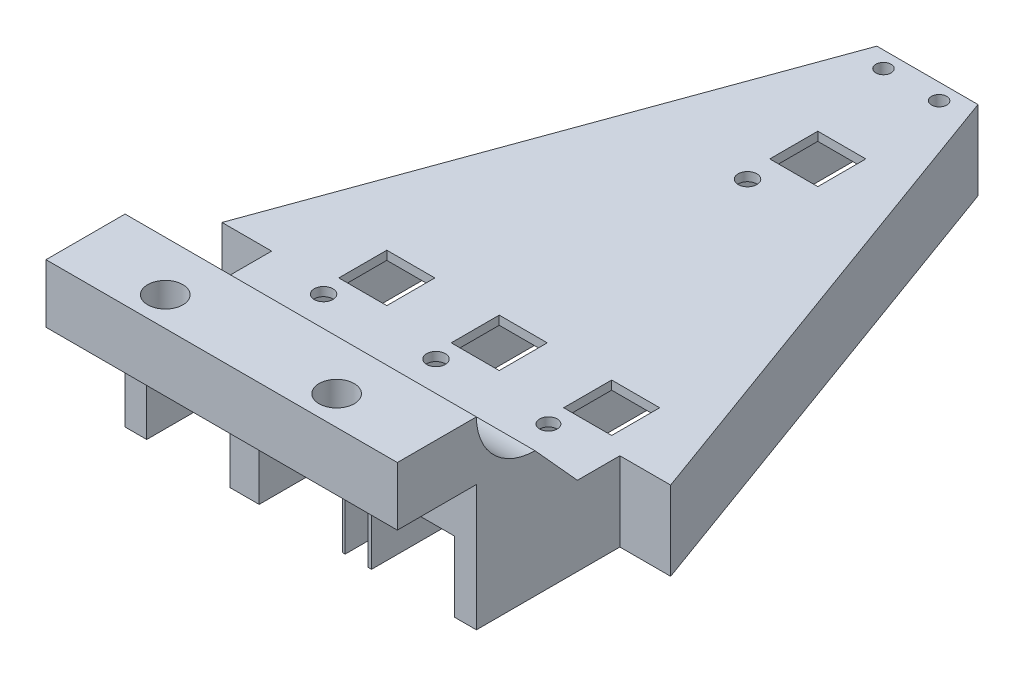
SolidWorks part; units mm, degrees
ref_plane "Front Plane" through (0, 0, 0) normal (0, 0, 1) x (1, 0, 0)
ref_plane "Top Plane" through (0, 0, 0) normal (0, 1, 0) x (1, 0, 0)
ref_plane "Right Plane" through (0, 0, 0) normal (1, 0, 0) x (0, 0, -1)
sketch "Sketch2" plane through (0, 0, 0) normal (0, 1, 0) x (1, 0, 0)
  line L1 (-15.37, -5) -> (44.63, -5)
  line L2 (-15.37, -5) -> (-15.37, 8.5)
  line L3 (-15.37, 8.5) -> (44.63, 8.5)
  line L4 (44.63, -5) -> (44.63, 8.5)
  circle A0 centre (0, 0) radius 1.75
  circle A1 centre (29.264, 0) radius 1.75
  point P12 (14.63, -5)
  dimension "D2" = 3.5
  dimension "D1" = 29.264
  dimension "D3" = 5
  dimension "D4" = 14.63
  dimension "D5" = 60
  dimension "D6" = 8.5
extrude "Boss-Extrude1" add sketch "Sketch2" along normal blind 10
sketch "Sketch4" plane through (0, 0, 0) normal (0, 1, 0) x (1, 0, 0)
  line L0 (-15.37, 8.5) -> (-15.37, 33.5337)
  line L1 (-15.37, 33.5337) -> (-23.8471, 33.5337)
  line L2 (-23.8471, 33.5337) -> (5.995, 115.5242)
  line L3 (53.3011, 33.0007) -> (23.265, 115.5242)
  line L4 (53.3011, 33.0007) -> (44.63, 33.0007)
  line L5 (44.63, 33.0007) -> (44.63, 8.5)
  line L6 (-15.37, -5) -> (44.63, -5) construction
  line L7 (7.53, 56.7) -> (21.73, 56.7)
  line L8 (7.53, 56.7) -> (7.53, 24.5)
  line L9 (7.53, 24.5) -> (21.73, 24.5)
  line L10 (21.73, 56.7) -> (21.73, 24.5)
  line L11 (26.73, 56.7) -> (40.93, 56.7)
  line L12 (26.73, 56.7) -> (26.73, 24.5)
  line L13 (26.73, 24.5) -> (40.93, 24.5)
  line L14 (40.93, 56.7) -> (40.93, 24.5)
  line L15 (-11.67, 56.7) -> (2.53, 56.7)
  line L16 (-11.67, 56.7) -> (-11.67, 24.5)
  line L17 (-11.67, 24.5) -> (2.53, 24.5)
  line L18 (2.53, 56.7) -> (2.53, 24.5)
  line L19 (7.53, 109.9) -> (21.73, 109.9)
  line L20 (7.53, 109.9) -> (7.53, 77.7)
  line L21 (7.53, 77.7) -> (21.73, 77.7)
  line L22 (21.73, 109.9) -> (21.73, 77.7)
  line L23 (23.265, 115.5242) -> (5.995, 115.5242)
  line L24 (44.63, 8.5) -> (-15.37, 8.5) construction
  line L25 (9.88, 112.7697) -> (19.38, 112.7697) construction
  circle A0 centre (9.88, 112.7697) radius 1.3
  circle A1 centre (19.38, 112.7697) radius 1.3
  point P23 (14.63, -5)
  point P24 (14.63, 56.7)
  point P29 (14.63, 109.9)
  point P30 (14.63, 77.7)
  point P31 (14.63, 115.5242)
  point P39 (14.63, 112.7697)
  dimension "D9" = 2.6
  dimension "D10" = 2.6
  dimension "D1" = 32.2
  dimension "D2" = 14.2
  dimension "D3" = 5
  dimension "D4" = 5
  dimension "D5" = 16
  dimension "D6" = 21
  dimension "D7" = 70
  dimension "D8" = 70
  dimension "D11" = 9.5
  dimension "D12" = 14.2
  dimension "D13" = 32.2
sketch "Sketch5" plane through (0, 0, 0) normal (0, 1, 0) x (1, 0, 0)
  line L0 (-15.37, 8.5) -> (-15.37, 33.5337) construction
  line L1 (-15.37, 33.5337) -> (-23.8471, 33.5337) construction
  line L2 (53.3011, 33.0007) -> (44.63, 33.0007) construction
  line L3 (44.63, 33.0007) -> (44.63, 8.5) construction
  line L4 (53.3011, 33.0007) -> (23.265, 115.5242) construction
  line L5 (23.265, 115.5242) -> (5.995, 115.5242) construction
  line L6 (-23.8471, 33.5337) -> (5.995, 115.5242) construction
  line L7 (-15.37, 8.5) -> (-15.37, 33.5337)
  line L8 (-15.37, 33.5337) -> (-23.8471, 33.5337)
  line L9 (53.3011, 33.0007) -> (44.63, 33.0007)
  line L10 (44.63, 33.0007) -> (44.63, 8.5)
  line L11 (53.3011, 33.0007) -> (23.265, 115.5242)
  line L12 (23.265, 115.5242) -> (5.995, 115.5242)
  line L13 (-23.8471, 33.5337) -> (5.995, 115.5242)
  line L14 (44.63, 8.5) -> (-15.37, 8.5) construction
  line L15 (44.63, 8.5) -> (-15.37, 8.5)
extrude "Boss-Extrude2" add sketch "Sketch5" against normal blind 21.5 separate body
sketch "Sketch8" plane through (-15.37, 0, 0) normal (-1, 0, 0) x (0, 0, 1)
  line L1 (-33.0007, 0) -> (-8.5, 0) construction
  line L2 (-8.5, 10) -> (-8.5, 0) construction
  line L3 (-18.5, 0) -> (-8.5, 0)
  line L4 (-8.5, 10) -> (-8.5, 0)
  arc A0 (-18.5, 0) -> (-8.5, 10) centre (-18.5, 10) ccw
extrude "Boss-Extrude3" add sketch "Sketch8" against normal up to surface (60 mm away) up to face at (44.63, 5, -1.75)
sketch "Sketch10" plane through (0, 0, 0) normal (0, 1, 0) x (1, 0, 0)
  line L0 (9.88, 112.7697) -> (19.38, 112.7697) construction
  line L1 (9.88, 112.7697) -> (19.38, 112.7697)
  circle A0 centre (19.38, 112.7697) radius 1.3 construction
  circle A1 centre (9.88, 112.7697) radius 1.3 construction
  circle A2 centre (19.38, 112.7697) radius 1.3
  circle A3 centre (9.88, 112.7697) radius 1.3
extrude "Cut-Extrude1" cut sketch "Sketch10" against normal through all
sketch "Sketch12" plane through (0, -21.5, 0) normal (0, -1, 0) x (1, 0, 0)
  line L0 (21.73, -109.9) -> (21.73, -77.7) construction
  line L1 (7.53, -109.9) -> (21.73, -109.9) construction
  line L2 (7.53, -77.7) -> (21.73, -77.7) construction
  line L3 (7.53, -109.9) -> (7.53, -77.7) construction
  line L4 (-11.67, -24.5) -> (2.53, -24.5) construction
  line L5 (-11.67, -56.7) -> (-11.67, -24.5) construction
  line L6 (-11.67, -56.7) -> (2.53, -56.7) construction
  line L7 (2.53, -56.7) -> (2.53, -24.5) construction
  line L8 (7.53, -56.7) -> (21.73, -56.7) construction
  line L9 (7.53, -56.7) -> (7.53, -24.5) construction
  line L10 (7.53, -24.5) -> (21.73, -24.5) construction
  line L11 (21.73, -56.7) -> (21.73, -24.5) construction
  line L12 (26.73, -24.5) -> (40.93, -24.5) construction
  line L13 (26.73, -56.7) -> (26.73, -24.5) construction
  line L14 (26.73, -56.7) -> (40.93, -56.7) construction
  line L15 (40.93, -56.7) -> (40.93, -24.5) construction
  line L16 (21.73, -109.9) -> (21.73, -77.7)
  line L17 (7.53, -109.9) -> (21.73, -109.9)
  line L18 (7.53, -77.7) -> (21.73, -77.7)
  line L19 (7.53, -109.9) -> (7.53, -77.7)
  line L20 (-11.67, -24.5) -> (2.53, -24.5)
  line L21 (-11.67, -56.7) -> (-11.67, -24.5)
  line L22 (-11.67, -56.7) -> (2.53, -56.7)
  line L23 (2.53, -56.7) -> (2.53, -24.5)
  line L24 (7.53, -56.7) -> (21.73, -56.7)
  line L25 (7.53, -56.7) -> (7.53, -24.5)
  line L26 (7.53, -24.5) -> (21.73, -24.5)
  line L27 (21.73, -56.7) -> (21.73, -24.5)
  line L28 (26.73, -24.5) -> (40.93, -24.5)
  line L29 (26.73, -56.7) -> (26.73, -24.5)
  line L30 (26.73, -56.7) -> (40.93, -56.7)
  line L31 (40.93, -56.7) -> (40.93, -24.5)
extrude "Cut-Extrude2" cut sketch "Sketch12" against normal blind 12
sketch "Sketch13" plane through (0, -21.5, 0) normal (0, -1, 0) x (1, 0, 0)
  line L0 (7.53, -109.9) -> (7.53, -77.7) construction
  line L1 (21.73, -77.7) -> (7.53, -77.7)
  line L2 (21.73, -77.7) -> (21.73, -61.7)
  line L4 (7.53, -77.7) -> (7.53, -61.7)
  line L5 (-15.37, -8.5) -> (44.63, -8.5) construction
  line L6 (26.73, -24.5) -> (40.93, -24.5)
  line L7 (26.73, -24.5) -> (26.73, -8.5)
  line L9 (40.93, -24.5) -> (40.93, -8.5)
  line L10 (40.93, -56.7) -> (40.93, -24.5) construction
  line L15 (7.53, -24.5) -> (21.73, -24.5)
  line L16 (7.53, -24.5) -> (7.53, -8.5)
  line L18 (21.73, -24.5) -> (21.73, -8.5)
  line L19 (-11.67, -24.5) -> (2.53, -24.5)
  line L20 (-11.67, -24.5) -> (-11.67, -8.5)
  line L22 (2.53, -24.5) -> (2.53, -8.5)
  line L26 (21.73, -56.7) -> (21.73, -24.5) construction
  line L27 (2.53, -56.7) -> (2.53, -24.5) construction
  line L28 (40.93, -8.5) -> (40.93, -5.0147)
  line L29 (21.73, -61.7) -> (26.1492, -61.7)
  line L30 (26.1492, -61.7) -> (26.1492, -8.5)
  line L31 (-15.37, -8.5) -> (44.63, -8.5) construction
  line L32 (-15.37, 5) -> (44.63, 5) construction
  line L33 (22.2238, -8.5) -> (22.2238, -57.397)
  line L34 (22.2238, -57.397) -> (7.53, -57.397)
  line L35 (7.53, -57.397) -> (7.53, -61.7)
  line L36 (40.93, -5.0147) -> (-11.67, -5.0147)
  line L37 (-11.67, -5.0147) -> (-11.67, -8.5)
  line L38 (26.73, -8.5) -> (26.1492, -8.5)
  line L39 (22.2238, -8.5) -> (21.73, -8.5)
  line L40 (7.53, -8.5) -> (2.53, -8.5)
  line L41 (18.5724, -5.0147) -> (10.6876, -5.0147)
  line L42 (18.5724, -5.0147) -> (18.5724, 5)
  line L43 (18.5724, 5) -> (10.6876, 5)
  line L44 (10.6876, -5.0147) -> (10.6876, 5)
  point P44 (14.63, -24.5)
  point P45 (14.63, 5)
extrude "Cut-Extrude3" cut sketch "Sketch13" against normal blind 12 contours L36 L37 L20 L19 L22 L40 L16 L15 L18 L39 L33 L34 L35 L4 L1 L2 L29 L30 L38 L7 L6 L9 L28
sketch "Sketch14" plane through (0, 10, 0) normal (0, 1, 0) x (1, 0, 0)
  circle A0 centre (0, 0) radius 3
  circle A1 centre (29.264, 0) radius 3
  dimension "D1" = 6
  dimension "D2" = 6
extrude "Cut-Extrude4" cut sketch "Sketch14" against normal offset from surface (6.5 mm away) 3.5 up to face at (14.63, 0, -1.75)
sketch "Sketch15" plane through (0, 0, 0) normal (0, 1, 0) x (1, 0, 0)
  line L0 (-11.67, 24.5) -> (2.53, 24.5) construction
  line L1 (-11.67, 56.7) -> (-11.67, 24.5) construction
  line L2 (2.53, 56.7) -> (2.53, 24.5) construction
  line L3 (-11.67, 56.7) -> (2.53, 56.7) construction
  line L4 (26.73, 56.7) -> (40.93, 56.7) construction
  line L5 (26.73, 56.7) -> (26.73, 24.5) construction
  line L6 (40.93, 56.7) -> (40.93, 24.5) construction
  line L7 (26.73, 24.5) -> (40.93, 24.5) construction
  line L8 (7.53, 56.7) -> (7.53, 24.5) construction
  line L9 (21.73, 56.7) -> (21.73, 24.5) construction
  line L10 (7.53, 24.5) -> (21.73, 24.5) construction
  line L11 (7.53, 56.7) -> (21.73, 56.7) construction
  line L12 (21.73, 109.9) -> (21.73, 77.7) construction
  line L13 (7.53, 109.9) -> (7.53, 77.7) construction
  line L14 (7.53, 109.9) -> (21.73, 109.9) construction
  line L15 (7.53, 77.7) -> (21.73, 77.7) construction
  line L16 (-11.67, 24.5) -> (2.53, 24.5) construction
  line L17 (-11.67, 56.7) -> (-11.67, 24.5) construction
  line L18 (2.53, 56.7) -> (2.53, 24.5) construction
  line L19 (-11.67, 56.7) -> (2.53, 56.7) construction
  line L20 (26.73, 56.7) -> (40.93, 56.7) construction
  line L21 (26.73, 56.7) -> (26.73, 24.5) construction
  line L22 (40.93, 56.7) -> (40.93, 24.5) construction
  line L23 (26.73, 24.5) -> (40.93, 24.5) construction
  line L24 (7.53, 56.7) -> (7.53, 24.5) construction
  line L25 (21.73, 56.7) -> (21.73, 24.5) construction
  line L26 (7.53, 24.5) -> (21.73, 24.5) construction
  line L27 (7.53, 56.7) -> (21.73, 56.7) construction
  line L28 (21.73, 109.9) -> (21.73, 77.7) construction
  line L29 (7.53, 109.9) -> (7.53, 77.7) construction
  line L30 (7.53, 109.9) -> (21.73, 109.9) construction
  line L31 (7.53, 77.7) -> (21.73, 77.7) construction
  line L33 (13.53, 89.7) -> (21.73, 89.7)
  line L34 (13.53, 89.7) -> (13.53, 97.9)
  line L35 (13.53, 97.9) -> (21.73, 97.9)
  line L36 (21.73, 89.7) -> (21.73, 97.9)
  line L37 (13.53, 43.5) -> (21.73, 43.5)
  line L38 (13.53, 43.5) -> (13.53, 35.3)
  line L39 (13.53, 35.3) -> (21.73, 35.3)
  line L40 (21.73, 43.5) -> (21.73, 35.3)
  line L41 (32.73, 43.5) -> (40.93, 43.5)
  line L42 (32.73, 43.5) -> (32.73, 35.3)
  line L43 (32.73, 35.3) -> (40.93, 35.3)
  line L44 (40.93, 43.5) -> (40.93, 35.3)
  line L45 (-5.67, 43.5) -> (2.53, 43.5)
  line L46 (-5.67, 43.5) -> (-5.67, 35.3)
  line L47 (-5.67, 35.3) -> (2.53, 35.3)
  line L48 (2.53, 43.5) -> (2.53, 35.3)
  circle A0 centre (-4.57, 31.6) radius 1.6
  circle A1 centre (14.63, 31.6) radius 1.6
  circle A2 centre (33.83, 31.6) radius 1.5
  circle A3 centre (14.63, 84.8) radius 1.6
  point P32 (21.73, 93.8)
  point P33 (21.73, 93.8)
  point P45 (33.83, 24.5)
  dimension "D8" = 3.2
  dimension "D9" = 3.2
  dimension "D10" = 3
  dimension "D14" = 7.1
  dimension "D16" = 3.2
  dimension "D1" = 8.2
  dimension "D2" = 8.2
  dimension "D3" = 8.2
  dimension "D4" = 8.2
  dimension "D5" = 8.2
  dimension "D6" = 7.1
  dimension "D7" = 7.1
  dimension "D11" = 7.1
  dimension "D12" = 7.1
  dimension "D13" = 7.1
  dimension "D15" = 7.1
  dimension "D17" = 19
extrude "Cut-Extrude5" cut sketch "Sketch15" against normal through all
sketch "Sketch16" plane through (0, 0, 0) normal (0, 1, 0) x (1, 0, 0)
  line L8 (-15.37, 18.5) -> (44.63, 18.5)
  line L9 (44.63, 18.5) -> (44.63, 33.0007)
  line L10 (44.63, 33.0007) -> (53.3011, 33.0007)
  line L11 (53.3011, 33.0007) -> (23.265, 115.5242)
  line L12 (23.265, 115.5242) -> (5.995, 115.5242)
  line L13 (5.995, 115.5242) -> (-23.8471, 33.5337)
  line L14 (-23.8471, 33.5337) -> (-15.37, 33.5337)
  line L15 (-15.37, 33.5337) -> (-15.37, 18.5)
  line L16 (-15.37, 18.5) -> (44.63, 18.5)
  line L17 (44.63, 18.5) -> (44.63, 33.0007)
  line L18 (44.63, 33.0007) -> (53.3011, 33.0007)
  line L19 (53.3011, 33.0007) -> (23.265, 115.5242)
  line L20 (23.265, 115.5242) -> (5.995, 115.5242)
  line L21 (5.995, 115.5242) -> (-23.8471, 33.5337)
  line L22 (-23.8471, 33.5337) -> (-15.37, 33.5337)
  line L23 (-15.37, 33.5337) -> (-15.37, 18.5)
  dimension "D1" = 0
extrude "Cut-Extrude6" cut sketch "Sketch16" against normal blind 8
sketch "Sketch17" plane through (44.63, 0, 0) normal (1, 0, 0) x (0, 0, -1)
  line L0 (18.5, 0) -> (25.7503, -8)
  line L1 (18.5, -8) -> (33.0007, -8) construction
  line L2 (18.5, 0) -> (18.5, -8)
  line L3 (18.5, -8) -> (25.7503, -8)
  arc A0 (8.5, 10) -> (18.5, 0) centre (18.5, 10) ccw construction
extrude "Boss-Extrude4" add sketch "Sketch17" against normal up to surface (60 mm away) up to face at (-15.37, -4.5635, -13.0552)
equation "\"block\"=10"
equation "\"D1@Boss-Extrude1\"=\"block\""
equation "\"RomiToEndOfSensor\"= 21.5"
equation "\"D1@Boss-Extrude2\"=\"RomiToEndOfSensor\""
equation "\"SensorHeight\"=12"
equation "\"D1@Cut-Extrude2\"=\"SensorHeight\""
